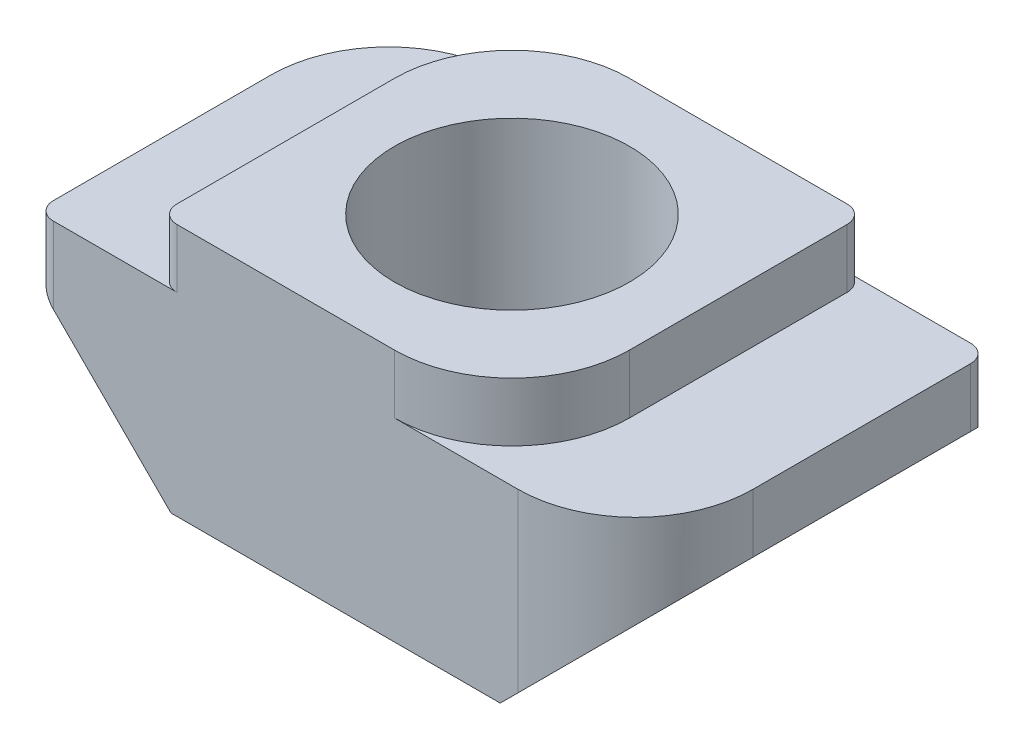
SolidWorks part; units mm, degrees
material "不锈钢 (铁素体)"
ref_plane "前视基准面" through (0, 0, 0) normal (0, 0, 1) x (1, 0, 0)
ref_plane "上视基准面" through (0, 0, 0) normal (0, 1, 0) x (1, 0, 0)
ref_plane "右视基准面" through (0, 0, 0) normal (1, 0, 0) x (0, 0, -1)
sketch "草图1" plane through (0, 0, 0) normal (0, 0, 1) x (1, 0, 0)
  line L0 (0, 0) -> (0, 8533.2886) construction
  line L1 (-3, 4.3) -> (3, 4.3)
  line L2 (3, 4.3) -> (3, 3.3)
  line L3 (3, 3.3) -> (5.1, 3.3)
  line L4 (5.1, 3.3) -> (5.1, 2.3)
  line L5 (5.1, 2.3) -> (2.8, 0)
  line L6 (2.8, 0) -> (-2.8, 0)
  line L7 (-5.1, 2.3) -> (-2.8, 0)
  line L8 (-5.1, 3.3) -> (-5.1, 2.3)
  line L9 (-3, 3.3) -> (-5.1, 3.3)
  line L10 (-3, 4.3) -> (-3, 3.3)
  point P11 (0, 0)
  point P15 (0, 4.3)
  dimension "D1" = 3.3
  dimension "D2" = 10.2
  dimension "D3" = 4.3
  dimension "D4" = 45
  dimension "D5" = 1
  dimension "D6" = 6
extrude "凸台-拉伸1" add sketch "草图1" along normal blind 6
fillet "圆角1" radius 2 2 edges at (3, 3.8, 6) (-3, 3.8, 0)
fillet "圆角2" radius 2 2 edges at (5.1, 2.8, 6) (-5.1, 2.8, 0)
fillet "圆角3" radius 0.3 4 edges at (-5.1, 2.8, 6) (-3, 3.8, 6) (3, 3.8, 0) (5.1, 2.8, 0)
sketch "草图2" plane through (0, 4.3, 0) normal (0, 1, 0) x (1, 0, 0)
  circle A0 centre (0, -3) radius 2
  dimension "D1" = 4
  dimension "D2" = 3
extrude "切除-拉伸1" cut sketch "草图2" against normal blind 6
